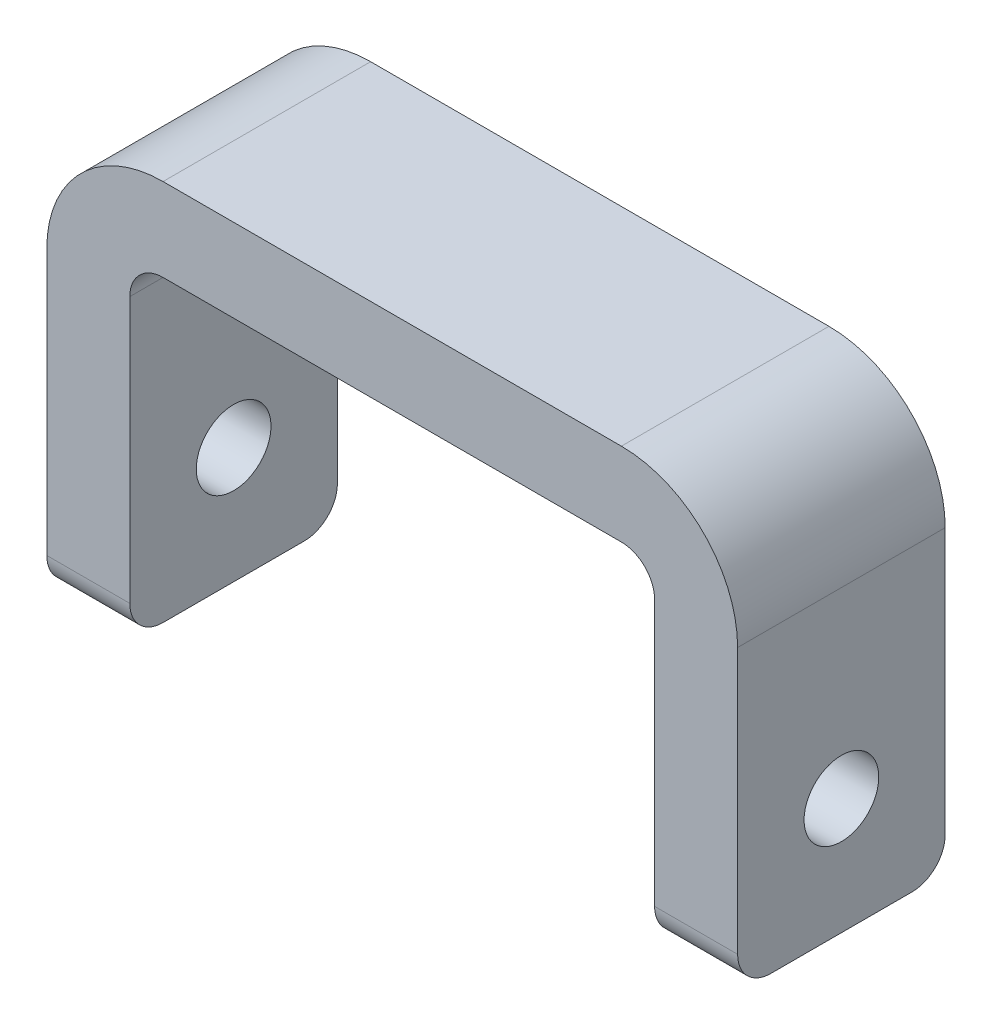
SolidWorks part; units mm, degrees
ref_plane "Front Plane" through (0, 0, 0) normal (0, 0, 1) x (1, 0, 0)
ref_plane "Top Plane" through (0, 0, 0) normal (0, 1, 0) x (1, 0, 0)
ref_plane "Right Plane" through (0, 0, 0) normal (1, 0, 0) x (0, 0, -1)
sketch "Sketch1" plane through (0, 0, 0) normal (0, 0, 1) x (1, 0, 0)
  line L0 (-15.8, 0) -> (-20.8, 0)
  line L1 (-20.8, 0) -> (-20.8, 25)
  line L2 (-20.8, 25) -> (20.8, 25)
  line L3 (-15.8, 0) -> (-15.8, 20)
  line L4 (-15.8, 20) -> (15.8, 20)
  line L5 (0, 0) -> (0, 11.8807) construction
  line L6 (15.8, 0) -> (15.8, 20)
  line L7 (20.8, 0) -> (20.8, 25)
  line L8 (15.8, 0) -> (20.8, 0)
  point P12 (0, 20)
  point P14 (0, 25)
  dimension "D1" = 31.6
  dimension "D2" = 5
  dimension "D3" = 5
  dimension "D4" = 20
extrude "Boss-Extrude1" add sketch "Sketch1" along normal mid plane 12.5
sketch "Sketch2" plane through (-20.8, 0, 0) normal (-1, 0, 0) x (0, 0, 1)
  line L0 (0, 0) -> (0, 25) construction
  line L1 (4.25, 0) -> (-4.25, 0) construction
  line L2 (6.25, 25) -> (-6.25, 25) construction
  circle A0 centre (0, 7) radius 3.05
  point P6 (0, 7)
  dimension "D1" = 6.1
  dimension "D2" = 7
fillet "Fillet1" radius 2 2 edges at (15.8, 20, 0) (-15.8, 20, 0)
fillet "Fillet2" radius 7 2 edges at (20.8, 25, 0) (-20.8, 25, 0)
fillet "Fillet3" radius 2 4 edges at (18.3, 0, -6.25) (18.3, 0, 6.25) (-18.3, 0, -6.25) (-18.3, 0, 6.25)
hole_wizard "M4 Clearance Hole1" positions "Sketch2" profile "Sketch3" hole size "M4" standard "ANSI Metric" end condition through all
sketch "Sketch3" plane through (-20.8, 7, 0) normal (0, 1, 0) x (0, 0, 1)
  line L0 (0, 0) -> (0, 41.6)
  line L1 (0, 41.6) -> (2.25, 41.6)
  line L2 (2.25, 41.6) -> (2.25, 0)
  line L5 (2.25, 0) -> (0, 0)
  line L11 (0, -6.35) -> (0, 107.95) construction
  dimension "Thru Hole Dia." = 4.5
  dimension "Thru Hole Depth" = 41.6
equation "\"D3@Sketch1\"=\"D2@Sketch1\""
